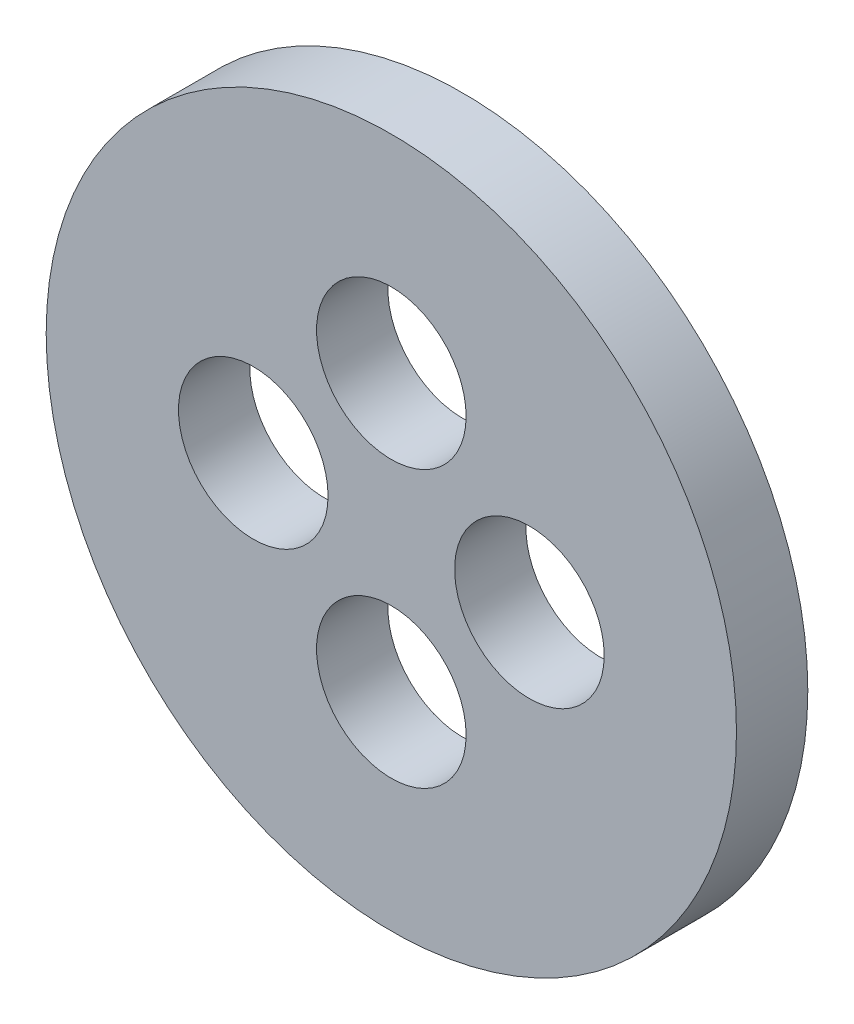
SolidWorks part; units mm, degrees
material "Teak"
ref_plane "Front Plane" through (0, 0, 0) normal (0, 0, 1) x (1, 0, 0)
ref_plane "Top Plane" through (0, 0, 0) normal (0, 1, 0) x (1, 0, 0)
ref_plane "Right Plane" through (0, 0, 0) normal (1, 0, 0) x (0, 0, -1)
sketch "Sketch1" plane through (0, 0, 0) normal (0, 0, 1) x (1, 0, 0)
  circle A0 centre (-6, 0) radius 3.25
  circle A1 centre (0, 0) radius 12.7
  circle A2 centre (0, 6) radius 3.25
  circle A3 centre (6, 0) radius 3.25
  circle A4 centre (0, -6) radius 3.25
  point P13 (0, 0)
  dimension "D1" = 6.5
  dimension "D2" = 25.4
  dimension "D4" = 12
  dimension "D5" = 0
  dimension "D6" = 0
  dimension "D3" = 4
extrude "Boss-Extrude1" add sketch "Sketch1" along normal blind 3.1
sketch "Sketch2" plane through (0, 0, 3.1) normal (0, 0, 1) x (1, 0, 0)
  circle A0 centre (0, 0) radius 12.7
  circle A1 centre (0, 0) radius 15
  dimension "D1" = 30
extrude "Boss-Extrude2" add sketch "Sketch2" against normal through all
sketch "Sketch3" plane through (0, 0, 3.1) normal (0, 0, 1) x (1, 0, 0)
  line L0 (0, 0) -> (0, 15) construction
  line L1 (0, 0) -> (10.6066, 10.6066) construction
  circle A0 centre (0, 0) radius 15 construction
  circle A1 centre (6.9148, 6.9148) radius 2
  circle A2 centre (6.9148, -6.9148) radius 2
  circle A3 centre (-6.9148, -6.9148) radius 2
  circle A4 centre (-6.9148, 6.9148) radius 2
  point P18 (0, 0)
  dimension "D2" = 4
  dimension "D1" = 45
  dimension "D3" = 4
  dimension "D4" = 19.558
  dimension "D5" = 0
extrude "Cut-Extrude1" [suppressed] cut sketch "Sketch3" against normal through all
equation "\"thick\"= 3.1mm"
equation "\"small_bearing_outer\"=12.9mm"
equation "\"servo1_L\"=40.7mm"
equation "\"servo1_W\"=20.5mm"
equation "\"servo1_H\"=43.5mm"
equation "\"servo1_hL\"=49mm"
equation "\"servo1_hW\"=10mm"
equation "\"servo1_H2\"=27mm"
equation "\"large_bearing_inner\"=2.75in"
equation "\"large_bearing_outer\"=4.75in"
equation "\"large_bearing_thick\"=3/8in"
equation "\"large_bearing_h1\"=3.25in"
equation "\"large_bearing_h2\"=4.25in"
equation "\"D1@Boss-Extrude1\"=\"thick\""
